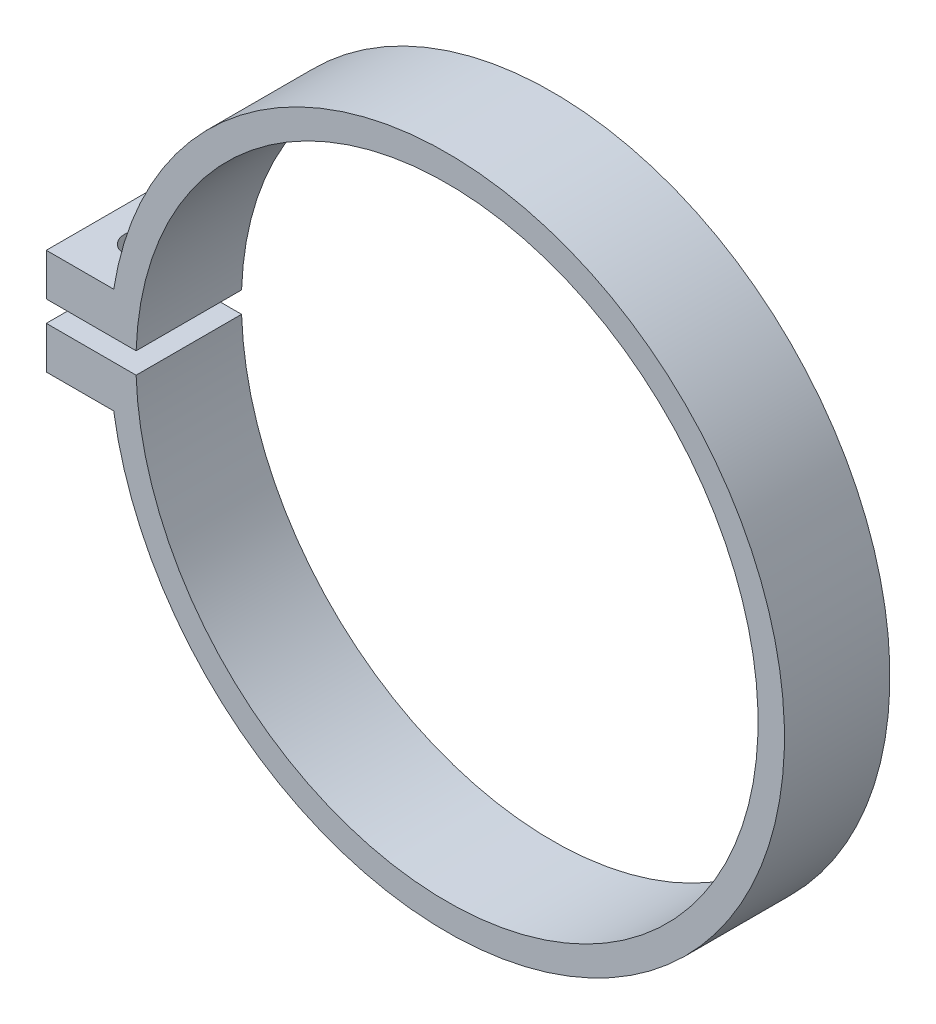
SolidWorks part; units mm, degrees
ref_plane "Front Plane" through (0, 0, 0) normal (0, 0, 1) x (1, 0, 0)
ref_plane "Top Plane" through (0, 0, 0) normal (0, 1, 0) x (1, 0, 0)
ref_plane "Right Plane" through (0, 0, 0) normal (1, 0, 0) x (0, 0, -1)
sketch "Sketch1" plane through (0, 0, 0) normal (0, 0, 1) x (1, 0, 0)
  line L0 (0, 0) -> (0, -50000) construction
  circle A1 centre (0, 0) radius 32
  dimension "D2" = 64
extrude "Boss-Extrude1" add sketch "Sketch1" along normal mid plane 10 contours A1
sketch "Sketch4" plane through (0, 0, 0) normal (0, 0, 1) x (1, 0, 0)
  line L1 (-38, 5) -> (0, 5)
  line L2 (-38, 5) -> (-38, -5)
  line L3 (-38, -5) -> (0, -5)
  line L4 (0, 5) -> (0, -5)
  line L5 (-38, 5) -> (0, -5) construction
  line L6 (-38, -5) -> (0, 5) construction
  point P0 (-19, 0)
  dimension "D1" = 38
  dimension "D2" = 10
extrude "Boss-Extrude2" add sketch "Sketch4" along normal mid plane 10
sketch "Sketch5" plane through (0, 0, 5) normal (0, 0, 1) x (1, 0, 0)
  line L0 (-38, 5) -> (-38, -5) construction
  line L1 (-38, 1) -> (0, 1)
  line L2 (-38, 1) -> (-38, -1)
  line L3 (-38, -1) -> (0, -1)
  line L4 (0, 1) -> (0, -1)
  line L5 (-38, 1) -> (0, -1) construction
  line L6 (-38, -1) -> (0, 1) construction
  circle A0 centre (0, 0) radius 29.5
  point P6 (-19, 0)
  dimension "D1" = 59
  dimension "D2" = 2
extrude "Cut-Extrude1" cut sketch "Sketch5" against normal blind 26.5 contours A0 | L3 L4 L1 L2
sketch "Sketch6" plane through (0, 5, 0) normal (0, 1, 0) x (1, 0, 0)
  line L0 (-38, -5) -> (-38, 5) construction
  circle A0 centre (-34, 0) radius 1.6
  dimension "D1" = 3.2
  dimension "D2" = 4
extrude "Cut-Extrude2" cut sketch "Sketch6" against normal up to surface (10 mm away) and the other way through all up to face at (-34.8035, -5, 0)
